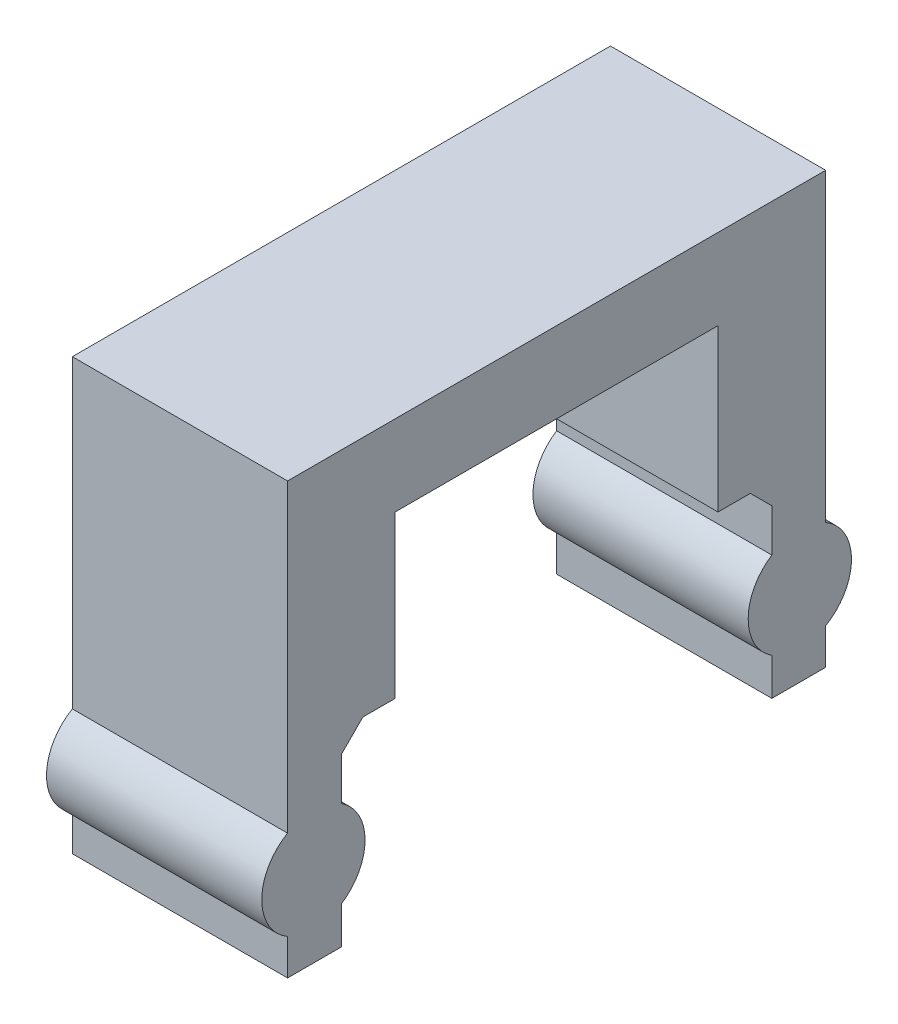
SolidWorks part; units mm, degrees
ref_plane "Front Plane" through (0, 0, 0) normal (0, 0, 1) x (1, 0, 0)
ref_plane "Top Plane" through (0, 0, 0) normal (0, 1, 0) x (1, 0, 0)
ref_plane "Right Plane" through (0, 0, 0) normal (1, 0, 0) x (0, 0, -1)
sketch "Sketch3" plane through (0, 0, 0) normal (1, 0, 0) x (0, 0, -1)
  line L0 (-101.8456, -12.2777) -> (-95.4956, -12.2777)
  line L1 (-95.4956, -12.2777) -> (-95.4956, 9.9473)
  line L2 (-95.4956, 9.9473) -> (-89.1456, 9.9473)
  line L3 (-89.1456, 9.9473) -> (-89.1456, 28.9973)
  line L4 (-89.1456, 28.9973) -> (-51.0456, 28.9973)
  line L5 (-51.0456, 28.9973) -> (-51.0456, 9.9473)
  line L6 (-51.0456, 9.9473) -> (-44.6956, 9.9473)
  line L7 (-44.6956, 9.9473) -> (-44.6956, -12.2777)
  line L8 (-44.6956, -12.2777) -> (-38.3456, -12.2777)
  line L9 (-38.3456, -12.2777) -> (-38.3456, 38.5223)
  line L10 (-38.3456, 38.5223) -> (-101.8456, 38.5223)
  line L11 (-101.8456, 38.5223) -> (-101.8456, -12.2777)
  dimension "D1" = 6.35
  dimension "D2" = 6.35
  dimension "D3" = 6.35
  dimension "D4" = 6.35
  dimension "D5" = 19.05
  dimension "D6" = 9.525
  dimension "D7" = 50.8
  dimension "D8" = 19.05
  dimension "D9" = 50.8
  dimension "D10" = 50.8
extrude "Boss-Extrude1" add sketch "Sketch3" along normal blind 25.4
sketch "Sketch4" plane through (25.4, 0, 0) normal (1, 0, 0) x (0, 0, -1)
  line L0 (-95.4956, 9.9473) -> (-89.1456, 9.9473) construction
  line L1 (-51.0456, 9.9473) -> (-44.6956, 9.9473) construction
  line L2 (-95.4956, -12.2777) -> (-95.4956, 9.9473) construction
  line L3 (-44.6956, 9.9473) -> (-44.6956, -12.2777) construction
  circle A0 centre (-98.7976, -2.7527) radius 6.096
  circle A1 centre (-41.3936, -2.7527) radius 6.096
  point P4 (-92.3206, 9.9473)
  dimension "D3" = 12.192
  dimension "D4" = 12.192
  dimension "D1" = 12.7
  dimension "D2" = 12.7
  dimension "D5" = 3.302
  dimension "D6" = 3.302
extrude "Boss-Extrude2" add sketch "Sketch4" against normal blind 25.4
chamfer "Chamfer1" distance 2.54 angle 45 2 edges at (12.7, 9.9473, 95.4956) (12.7, 9.9473, 44.6956)
